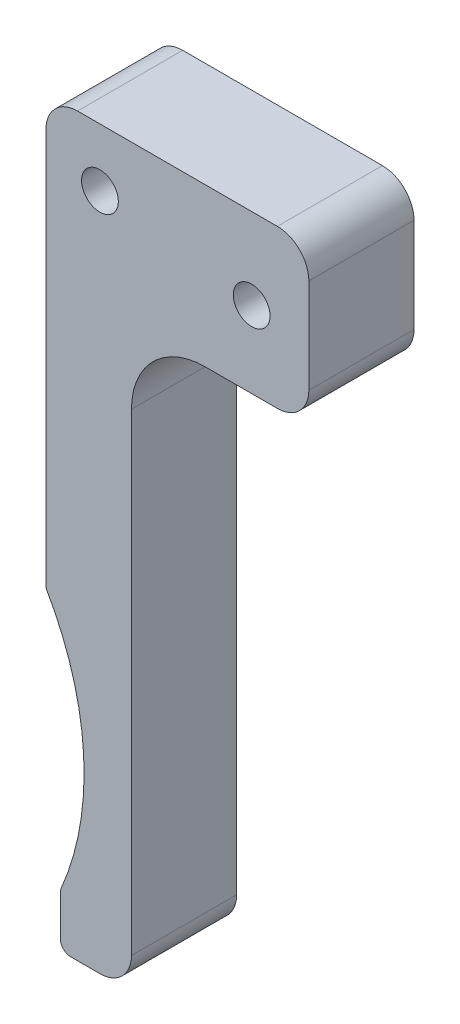
SolidWorks part; units mm, degrees
material "6063-T5"
ref_plane "Front Plane" through (0, 0, 0) normal (0, 0, 1) x (1, 0, 0)
ref_plane "Top Plane" through (0, 0, 0) normal (0, 1, 0) x (1, 0, 0)
ref_plane "Right Plane" through (0, 0, 0) normal (1, 0, 0) x (0, 0, -1)
sketch "Sketch1" plane through (0, 0, 0) normal (0, 0, 1) x (1, 0, 0)
  line L0 (19.5793, 58.738) -> (97.8967, 58.738) construction
  line L1 (92.5265, 102.6527) -> (111.5265, 102.6527)
  line L2 (41.1958, 130.7586) -> (191.1958, 130.7586) construction
  line L3 (114.5265, 99.6527) -> (114.5265, 90.6527)
  line L4 (111.5265, 87.6527) -> (104.6557, 87.6527)
  line L5 (97.6557, 80.6527) -> (97.6557, 35.6527)
  line L6 (94.6557, 32.6527) -> (91.8836, 32.6527)
  line L7 (90.8836, 33.6527) -> (90.8836, 37.4443)
  line L8 (89.5265, 99.6527) -> (89.5265, 61.8526)
  arc A0 (89.5265, 61.8526) -> (90.9653, 37.8402) centre (66.4272, 48.4192) cw
  arc A1 (114.5265, 99.6527) -> (111.5265, 102.6527) centre (111.5265, 99.6527) ccw
  arc A2 (111.5265, 87.6527) -> (114.5265, 90.6527) centre (111.5265, 90.6527) ccw
  arc A3 (97.6557, 80.6527) -> (104.6557, 87.6527) centre (104.6557, 80.6527) cw
  arc A4 (89.5265, 99.6527) -> (92.5265, 102.6527) centre (92.5265, 99.6527) cw
  arc A5 (97.6557, 35.6527) -> (94.6557, 32.6527) centre (94.6557, 35.6527) cw
  arc A6 (90.8836, 33.6527) -> (91.8836, 32.6527) centre (91.8836, 33.6527) ccw
  arc A7 (90.8836, 37.4443) -> (90.9653, 37.8402) centre (91.8836, 37.4443) cw
  circle A8 centre (94.6557, 97.1316) radius 1.75
  circle A9 centre (109.087, 94.9217) radius 1.75
  point P15 (114.5265, 102.6527)
  point P22 (89.5265, 102.6527)
  point P27 (90.8836, 32.6527)
  point P30 (90.8836, 37.6527)
  dimension "D2" = 3
  dimension "D3" = 3
  dimension "D4" = 7
  dimension "D5" = 3
  dimension "D6" = 3
  dimension "D10" = 1
  dimension "D11" = 3.5
  dimension "D12" = 3.5
  dimension "D1" = 25
  dimension "D7" = 70
  dimension "D8" = 15
  dimension "D9" = 5
extrude "Boss-Extrude1" add sketch "Sketch1" along normal blind 10
